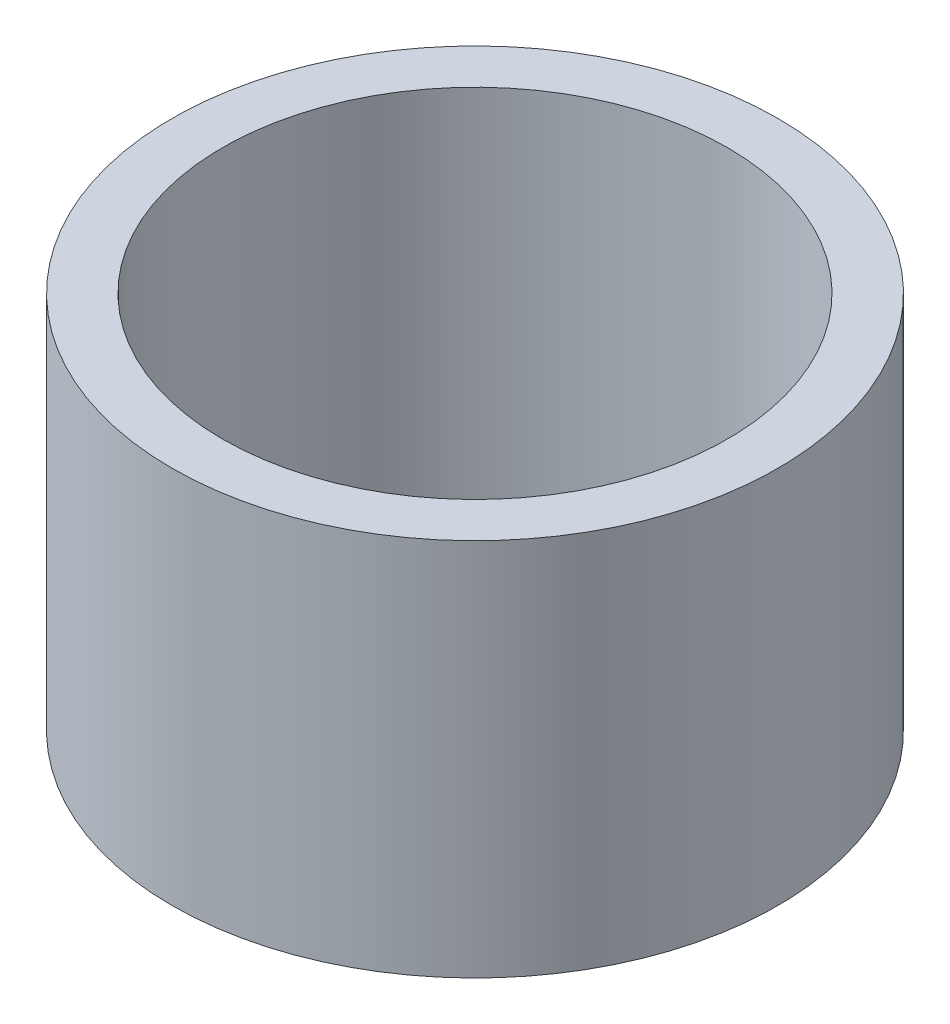
SolidWorks part; units mm, degrees
ref_plane "Front Plane" through (0, 0, 0) normal (0, 0, 1) x (1, 0, 0)
ref_plane "Top Plane" through (0, 0, 0) normal (0, 1, 0) x (1, 0, 0)
ref_plane "Right Plane" through (0, 0, 0) normal (1, 0, 0) x (0, 0, -1)
sketch "Sketch1" plane through (0, 0, 0) normal (0, 1, 0) x (1, 0, 0)
  circle A0 centre (0, 0) radius 400
  circle A1 centre (0, 0) radius 480
  dimension "D1" = 800
  dimension "D2" = 80
extrude "Boss-Extrude1" add sketch "Sketch1" along normal blind 600
